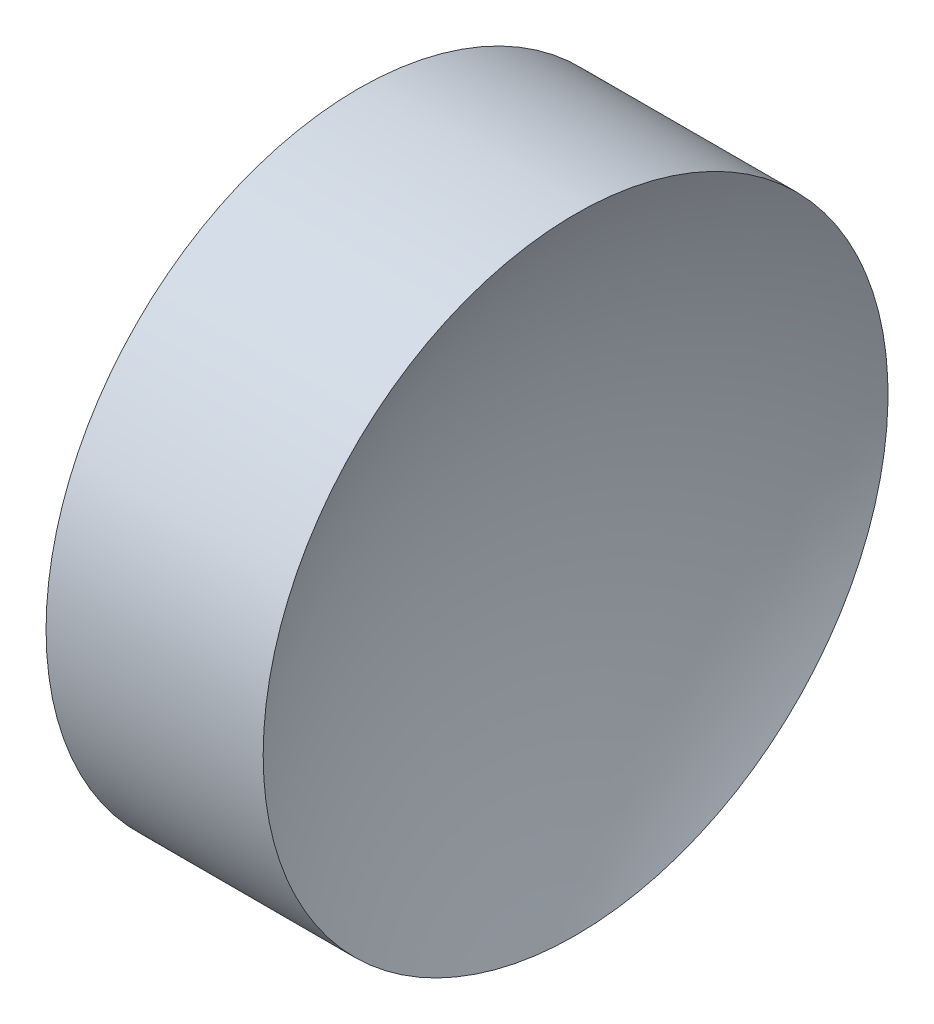
SolidWorks part; units mm, degrees
ref_plane "前视基准面" through (0, 0, 0) normal (0, 0, 1) x (1, 0, 0)
ref_plane "上视基准面" through (0, 0, 0) normal (0, 1, 0) x (1, 0, 0)
ref_plane "右视基准面" through (0, 0, 0) normal (1, 0, 0) x (0, 0, -1)
sketch "草图1" plane through (0, 0, 0) normal (0, 0, 1) x (1, 0, 0)
  line L0 (42.4499, 26.089) -> (55.6645, 26.089) construction
  line L1 (47.2916, 26.089) -> (48.7916, 26.089)
  line L3 (48.0416, 34.089) -> (50.8214, 34.089)
  line L4 (48.0416, 34.089) -> (45.2618, 34.089)
  arc A0 (50.8214, 34.089) -> (48.7916, 26.089) centre (65.5716, 26.089) ccw
  arc A1 (47.2916, 26.089) -> (45.2618, 34.089) centre (30.5116, 26.089) ccw
revolve "旋转1" add sketch "草图1" angle 360 about L0
